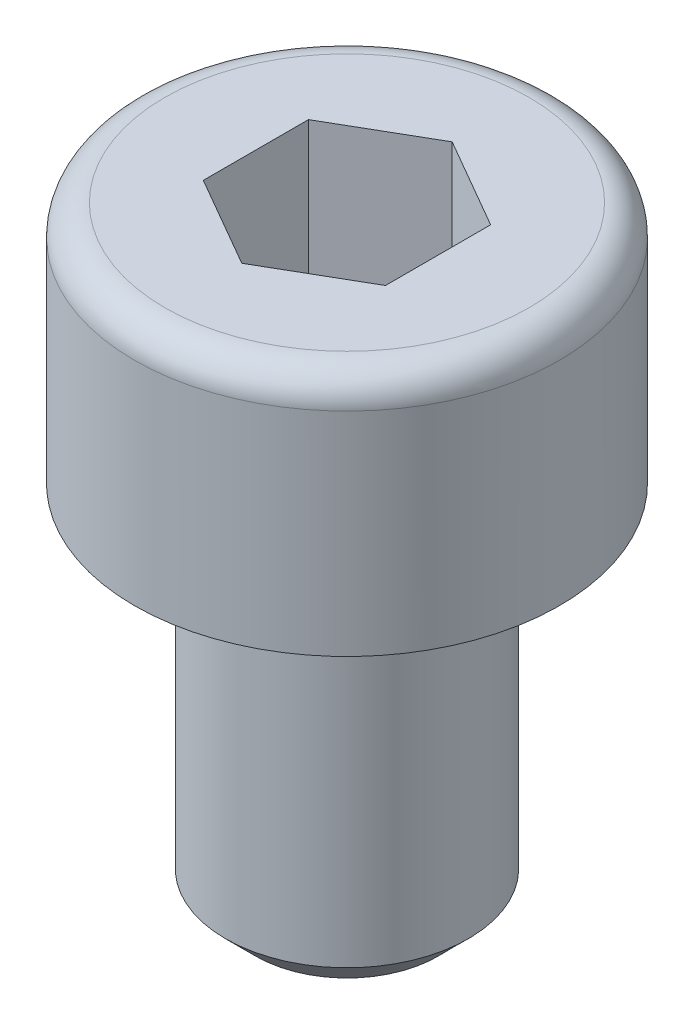
SolidWorks part; units mm, degrees
material "acero"
ref_plane "Alzado" through (0, 0, 0) normal (0, 0, 1) x (1, 0, 0)
ref_plane "Planta" through (0, 0, 0) normal (0, 1, 0) x (1, 0, 0)
ref_plane "Vista lateral" through (0, 0, 0) normal (1, 0, 0) x (0, 0, -1)
sketch "Croquis1" plane through (0, 0, 0) normal (0, 0, 1) x (1, 0, 0)
  line L0 (0, 0) -> (0, -60.9498) construction
  line L1 (0, 0) -> (3.5, 0)
  line L2 (3.5, 0) -> (3.5, -4)
  line L3 (3.5, -4) -> (2, -4)
  line L4 (2, -4) -> (2, -10)
  line L5 (2, -10) -> (0, -10)
  line L6 (0, -10) -> (0, 0)
  dimension "D1" = 6
  dimension "D2" = 4
  dimension "D3" = 7
  dimension "D4" = 4
revolve "Revolución1" add sketch "Croquis1" angle 360 about L0
sketch "Croquis2" plane through (0, 0, 0) normal (0, 1, 0) x (1, 0, 0)
  line L1 (1.5, 0.866) -> (0, 1.7321)
  line L2 (0, 1.7321) -> (-1.5, 0.866)
  line L3 (-1.5, 0.866) -> (-1.5, -0.866)
  line L4 (-1.5, -0.866) -> (0, -1.7321)
  line L5 (0, -1.7321) -> (1.5, -0.866)
  line L6 (1.5, -0.866) -> (1.5, 0.866)
  circle A0 centre (0, 0) radius 1.5 construction
  dimension "D1" = 3
extrude "Cortar-Extruir1" cut sketch "Croquis2" against normal blind 3
chamfer "Chaflán1" distance 0.5 angle 45 1 edges at (0, -10, 2)
fillet "Redondeo1" radius 0.5 1 edges at (0, 0, 3.5)
